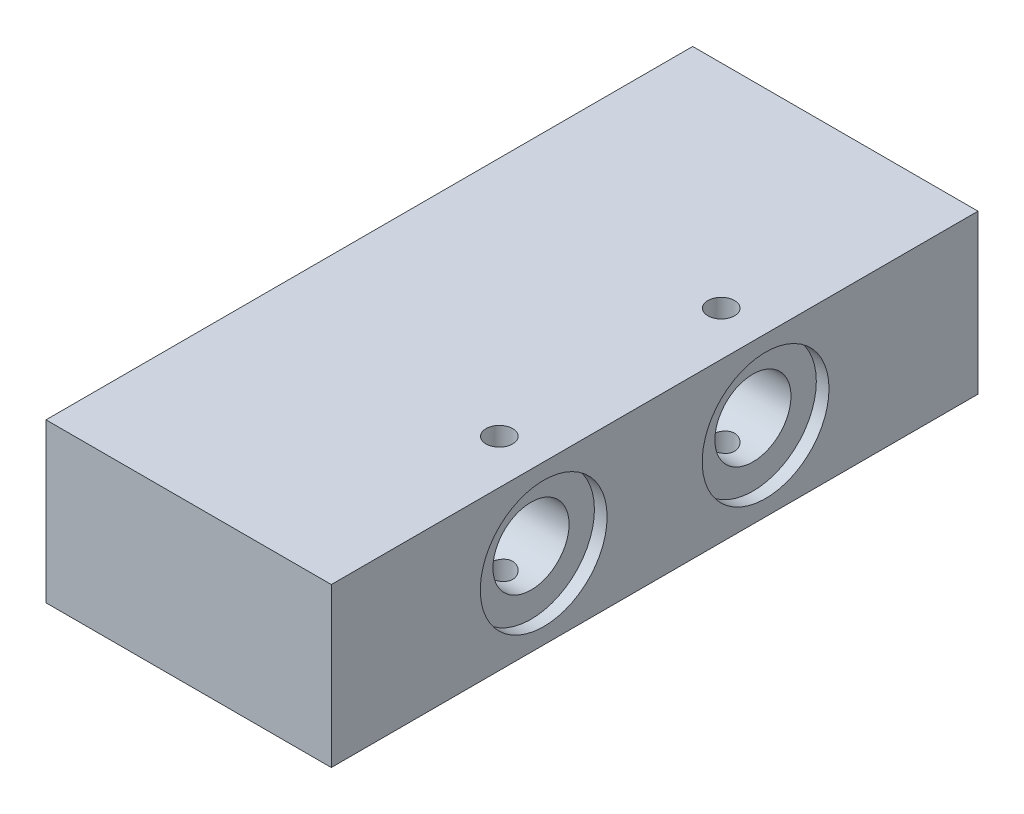
SolidWorks part; units mm, degrees
ref_plane "Front Plane" through (0, 0, 0) normal (0, 0, 1) x (1, 0, 0)
ref_plane "Top Plane" through (0, 0, 0) normal (0, 1, 0) x (1, 0, 0)
ref_plane "Right Plane" through (0, 0, 0) normal (1, 0, 0) x (0, 0, -1)
sketch "Sketch1" plane through (0, 0, 0) normal (0, 1, 0) x (1, 0, 0)
  line L1 (-22.5, -51) -> (22.5, -51)
  line L2 (-22.5, -51) -> (-22.5, 51)
  line L3 (-22.5, 51) -> (22.5, 51)
  line L4 (22.5, -51) -> (22.5, 51)
  line L5 (-22.5, -51) -> (22.5, 51) construction
  line L6 (-22.5, 51) -> (22.5, -51) construction
  point P0 (0, 0)
  dimension "D1" = 45
  dimension "D2" = 102
extrude "Boss-Extrude1" add sketch "Sketch1" along normal blind 25
hole_wizard "M5 Tapped Hole3" positions "Sketch12" profile "Sketch13" tap size "M5" standard "DIN" end condition through all
sketch "Sketch12" plane through (0, 25, 0) normal (0, 1, 0) x (1, 0, 0)
  line L0 (22.5, -51) -> (22.5, 51) construction
  line L1 (-22.5, -51) -> (22.5, -51) construction
  point P0 (15.5, 17.5)
  point P2 (15.5, -17.5)
  dimension "D1" = 7
  dimension "D2" = 7
  dimension "D3" = 33.5
  dimension "D4" = 35
sketch "Sketch13" plane through (15.5, 25, -17.5) normal (1, 0, 0) x (0, 0, 1)
  line L0 (0, 0) -> (0, 25)
  line L1 (0, 25) -> (2.1, 25)
  line L2 (2.1, 25) -> (2.1, 0)
  line L5 (2.1, 0) -> (0, 0)
  line L11 (0, -6.35) -> (0, 107.95) construction
  dimension "Thru Tap Drill Dia." = 4.2
  dimension "Thru Tap Drill Depth" = 25
cosmetic thread "Hole Thread9" parameters "D2"=5
cosmetic thread "Hole Thread10" parameters "D2"=5
sketch "Sketch27" plane through (-22.5, 0, 0) normal (-1, 0, 0) x (0, 0, 1)
  line L0 (51, 25) -> (51, 0) construction
  line L1 (-51, 25) -> (51, 25) construction
  circle A0 centre (-17.5, 12.5) radius 6
  circle A1 centre (17.5, 12.5) radius 6
  dimension "D1" = 12
  dimension "D2" = 12
  dimension "D5" = 12.5
  dimension "D3" = 33.5
  dimension "D4" = 35
  dimension "D6" = 12.5
extrude "Cut-Extrude1" cut sketch "Sketch27" against normal blind 74
sketch "Sketch28" plane through (-22.5, 0, 0) normal (-1, 0, 0) x (0, 0, 1)
  circle A0 centre (-17.5, 12.5) radius 10
  circle A1 centre (17.5, 12.5) radius 10
  dimension "D1" = 20
  dimension "D2" = 20
extrude "Cut-Extrude3" cut sketch "Sketch28" against normal blind 2
sketch "Sketch30" plane through (22.5, 0, 0) normal (1, 0, 0) x (0, 0, -1)
  circle A0 centre (-17.5, 12.5) radius 10
  circle A1 centre (17.5, 12.5) radius 10
  dimension "D1" = 20
  dimension "D2" = 20
extrude "Cut-Extrude4" cut sketch "Sketch30" against normal blind 2
hole_wizard "M5 Tapped Hole4" positions "Sketch31" profile "Sketch32" tap size "M5" standard "DIN"
sketch "Sketch31" plane through (0, 0, -51) normal (0, 0, -1) x (-1, 0, 0)
  line L0 (22.5, 25) -> (22.5, 0) construction
  line L1 (-22.5, 25) -> (-22.5, 0) construction
  line L3 (-22.5, 0) -> (22.5, 0) construction
  line L4 (-22.5, 25) -> (22.5, 25) construction
  point P0 (-18, 5)
  point P2 (18, 20)
  dimension "D1" = 4.5
  dimension "D2" = 4.5
  dimension "D3" = 5
  dimension "D4" = 5
sketch "Sketch32" plane through (18, 5, -51) normal (1, 0, 0) x (0, 1, 0)
  line L0 (0, 0) -> (0, 15.2618)
  line L1 (0, 15.2618) -> (2.1, 14)
  line L2 (2.1, 14) -> (2.1, 0)
  line L5 (2.1, 0) -> (0, 0)
  line L10 (0, 15.2618) -> (-2.1, 14) construction
  line L11 (0, -6.35) -> (0, 107.95) construction
  dimension "Tap Drill Dia." = 4.2
  dimension "Tap Drill Depth" = 14
  dimension "Drill Angle" = 118
cosmetic thread "Hole Thread11" parameters "D1"=10, "D2"=5
cosmetic thread "Hole Thread12" parameters "D1"=10, "D2"=5
hole_wizard "M5 Tapped Hole5" positions "Sketch33" profile "Sketch34" tap size "M5" standard "DIN"
sketch "Sketch33" plane through (-22.5, 0, 0) normal (-1, 0, 0) x (0, 0, 1)
  line L0 (-51, 0) -> (51, 0) construction
  point P0 (0, 12.5)
  dimension "D1" = 12.5
sketch "Sketch34" plane through (-22.5, 12.5, 0) normal (0, 1, 0) x (0, 0, 1)
  line L0 (0, 0) -> (0, 16.2618)
  line L1 (0, 16.2618) -> (2.1, 15)
  line L2 (2.1, 15) -> (2.1, 0)
  line L5 (2.1, 0) -> (0, 0)
  line L10 (0, 16.2618) -> (-2.1, 15) construction
  line L11 (0, -6.35) -> (0, 107.95) construction
  dimension "Tap Drill Dia." = 4.2
  dimension "Tap Drill Depth" = 15
  dimension "Drill Angle" = 118
cosmetic thread "Hole Thread13" parameters "D1"=10, "D2"=5
